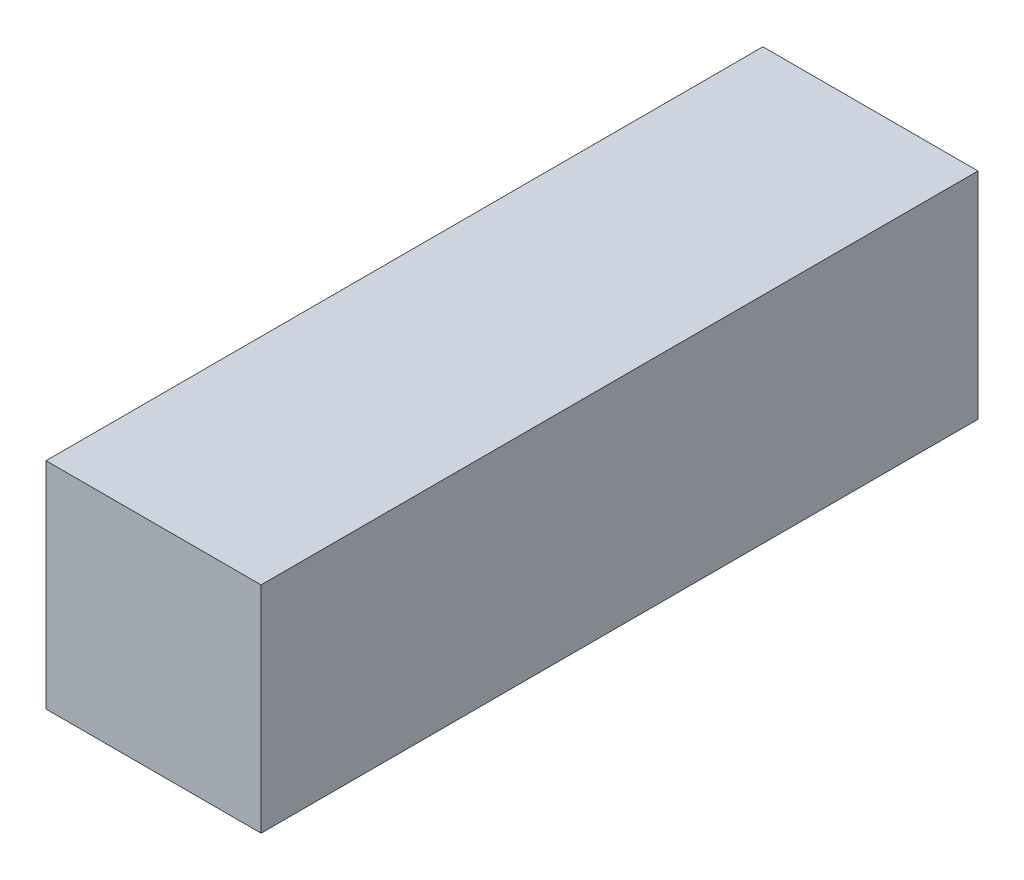
SolidWorks part; units mm, degrees
ref_plane "Face" through (0, 0, 0) normal (0, 0, 1) x (1, 0, 0)
ref_plane "Dessus" through (0, 0, 0) normal (0, 1, 0) x (1, 0, 0)
ref_plane "Droite" through (0, 0, 0) normal (1, 0, 0) x (0, 0, -1)
sketch "Esquisse1" plane through (0, 0, 0) normal (0, 0, 1) x (1, 0, 0)
  line L1 (0, 0) -> (18, 0)
  line L2 (0, 0) -> (0, 18)
  line L3 (0, 18) -> (18, 18)
  line L4 (18, 0) -> (18, 18)
  dimension "D1" = 18
  dimension "D2" = 18
extrude "Extrusion1" add sketch "Esquisse1" against normal blind 60
